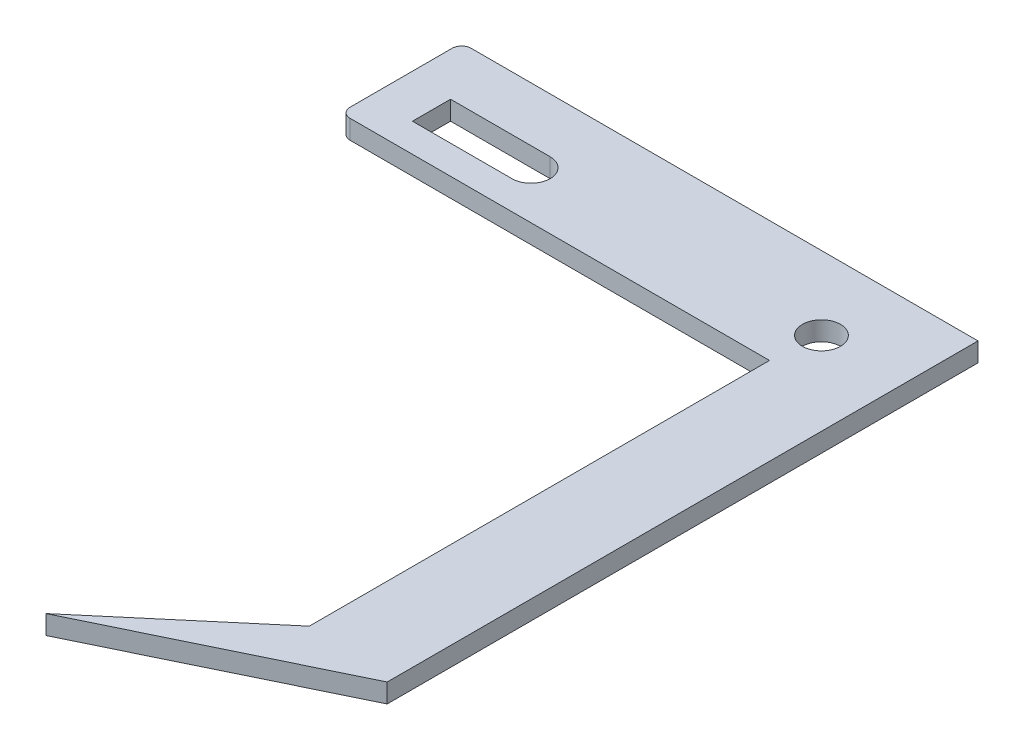
SolidWorks part; units mm, degrees
ref_plane "Front Plane" through (0, 0, 0) normal (0, 0, 1) x (1, 0, 0)
ref_plane "Top Plane" through (0, 0, 0) normal (0, 1, 0) x (1, 0, 0)
ref_plane "Right Plane" through (0, 0, 0) normal (1, 0, 0) x (0, 0, -1)
sketch "Sketch1" plane through (0, 0, 0) normal (0, 1, 0) x (1, 0, 0)
  line L0 (0, 48.4129) -> (0, 37.692)
  line L1 (1, 36.692) -> (31.48, 36.692)
  line L2 (15, 41.7006) -> (15, -27.2696) construction
  line L3 (31.48, 36.692) -> (43.0365, 36.692)
  line L4 (43.0365, 36.692) -> (43.0365, -13.308)
  line L5 (54.2008, -12.6029) -> (54.2008, 10.2676)
  line L6 (1, 49.4129) -> (41.48, 49.4129)
  line L7 (41.48, 49.4129) -> (54.2008, 49.4129)
  line L9 (15, 43.7006) -> (4.5495, 43.7006)
  line L10 (4.5495, 43.7006) -> (4.5495, 39.7006)
  line L11 (4.5495, 39.7006) -> (15, 39.7006)
  line L13 (30.0717, -24.2882) -> (36, -19.2674)
  line L15 (54.2008, 49.4129) -> (54.2008, 10.2676)
  line L17 (38.3103, -17.3107) -> (43.0365, -13.308)
  line L19 (36, -19.2674) -> (34.2536, -17.3107)
  line L20 (30.0717, -24.2882) -> (54.2008, -12.6029)
  line L21 (34.2536, -17.3107) -> (38.3103, -17.3107)
  arc A4 (1, 36.692) -> (0, 37.692) centre (1, 37.692) cw
  arc A5 (1, 49.4129) -> (0, 48.4129) centre (1, 48.4129) ccw
  arc A6 (15, 39.7006) -> (15, 43.7006) centre (15, 41.7006) ccw
  circle A7 centre (45.48, 41.7006) radius 2
  point P9 (36, 36.692)
  point P18 (0, 36.692)
  point P21 (0, 49.4129)
  dimension "D5" = 40.48
  dimension "D7" = 1
  dimension "D8" = 15
  dimension "D10" = 4
  dimension "D11" = 30.48
extrude "Boss-Extrude2" add sketch "Sketch1" along normal blind 2
sketch "Sketch2" plane through (0, 2, 0) normal (0, 1, 0) x (1, 0, 0)
ref_plane "Plane1" through (1, 2, -36.692) normal (1, 0, 0) x (0, 0, -1)
sketch "Sketch5" plane through (10.4655, 0, -9.341) normal (-0.7461, 0, 0.6659) x (0.6659, 0, 0.7461)
  line L0 (38.3465, 0) -> (38.3465, 2)
  line L1 (38.3465, 2) -> (35.7238, 2)
  line L2 (35.7238, 2) -> (35.7238, 0)
  line L3 (35.7238, 0) -> (38.3465, 0)
sketch "Sketch6" plane through (0, 2, 0) normal (0, 1, 0) x (1, 0, 0)
  line L0 (36, -19.2674) -> (38.3103, -17.3107)
  line L2 (38.3103, -17.3107) -> (34.2536, -17.3107)
  line L3 (34.2536, -17.3107) -> (36, -19.2674)
extrude "Cut-Extrude2" cut sketch "Sketch6" against normal blind 9
sketch "Sketch8" plane through (0, 2, 0) normal (0, 1, 0) x (1, 0, 0)
  line L0 (43.0365, 36.692) -> (45.0365, 36.692)
  line L1 (1, 36.692) -> (43.0365, 36.692) construction
  line L2 (45.0365, 36.692) -> (45.0365, -11.1155)
  line L3 (43.0365, -13.308) -> (45.0365, -11.6141)
  line L4 (43.0365, -13.308) -> (30.0717, -24.2882) construction
  line L5 (45.0365, -11.1155) -> (45.0365, -11.6141)
  line L6 (43.0365, -13.308) -> (43.0365, 36.692)
extrude "Cut-Extrude3" cut sketch "Sketch8" against normal blind 9
